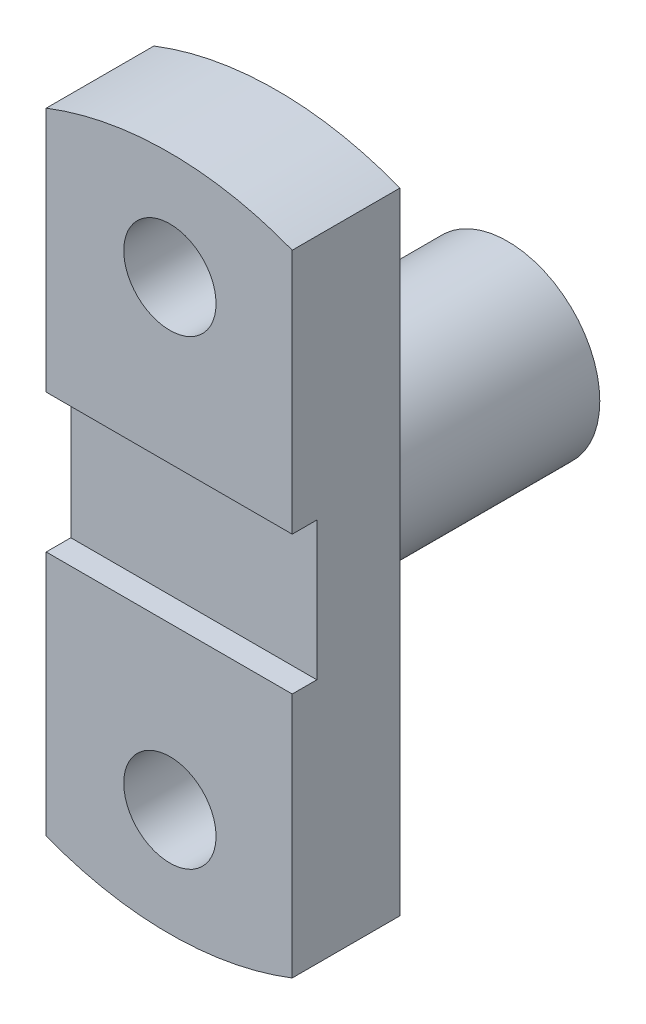
SolidWorks part; units mm, degrees
ref_plane "Front Plane" through (0, 0, 0) normal (0, 0, 1) x (1, 0, 0)
ref_plane "Top Plane" through (0, 0, 0) normal (0, 1, 0) x (1, 0, 0)
ref_plane "Right Plane" through (0, 0, 0) normal (1, 0, 0) x (0, 0, -1)
sketch "Sketch1" plane through (0, 0, 0) normal (0, 0, 1) x (1, 0, 0)
  line L0 (-137.6051, 0) -> (138.0407, 0) construction
  line L2 (40, -102.4695) -> (40, 102.4695)
  line L4 (-40, -102.4695) -> (-40, 102.4695)
  line L5 (40, -102.4695) -> (-40, 102.4695) construction
  line L6 (40, 102.4695) -> (-40, -102.4695) construction
  line L7 (-137.6051, 75) -> (138.0407, 75) construction
  line L8 (-137.6051, -75) -> (138.0407, -75) construction
  line L9 (0, 125.5156) -> (0, -138.3108) construction
  arc A0 (-40, -102.4695) -> (40, -102.4695) centre (0, 0) ccw
  arc A1 (40, 102.4695) -> (-40, 102.4695) centre (0, 0) ccw
  circle A2 centre (0.2178, 75) radius 15
  circle A3 centre (0.2178, -75) radius 15
  dimension "D1" = 220
  dimension "D5" = 30
  dimension "D6" = 0.2178
  dimension "D2" = 80
  dimension "D3" = 150
  dimension "D4" = 75
extrude "Boss-Extrude1" add sketch "Sketch1" along normal blind 35
sketch "Sketch2" plane through (40, 0, 0) normal (1, 0, 0) x (0, 0, -1)
  line L0 (-133.3783, 0) -> (131.5282, 0) construction
  line L1 (-35, 22.5) -> (-27, 22.5)
  line L2 (-35, -102.4695) -> (-35, 102.4695) construction
  line L3 (-27, 22.5) -> (-27, -22.5)
  line L4 (-27, -22.5) -> (-35, -22.5)
  line L5 (-35, -22.5) -> (-35, 22.5)
  point P8 (-35, 0)
  dimension "D1" = 45
  dimension "D2" = 8
extrude "Cut-Extrude1" cut sketch "Sketch2" against normal blind 85
sketch "Sketch3" plane through (0, 0, 0) normal (0, 0, -1) x (-1, 0, 0)
  circle A0 centre (0, 0) radius 30
  dimension "D1" = 60
extrude "Boss-Extrude2" add sketch "Sketch3" along normal blind 75
